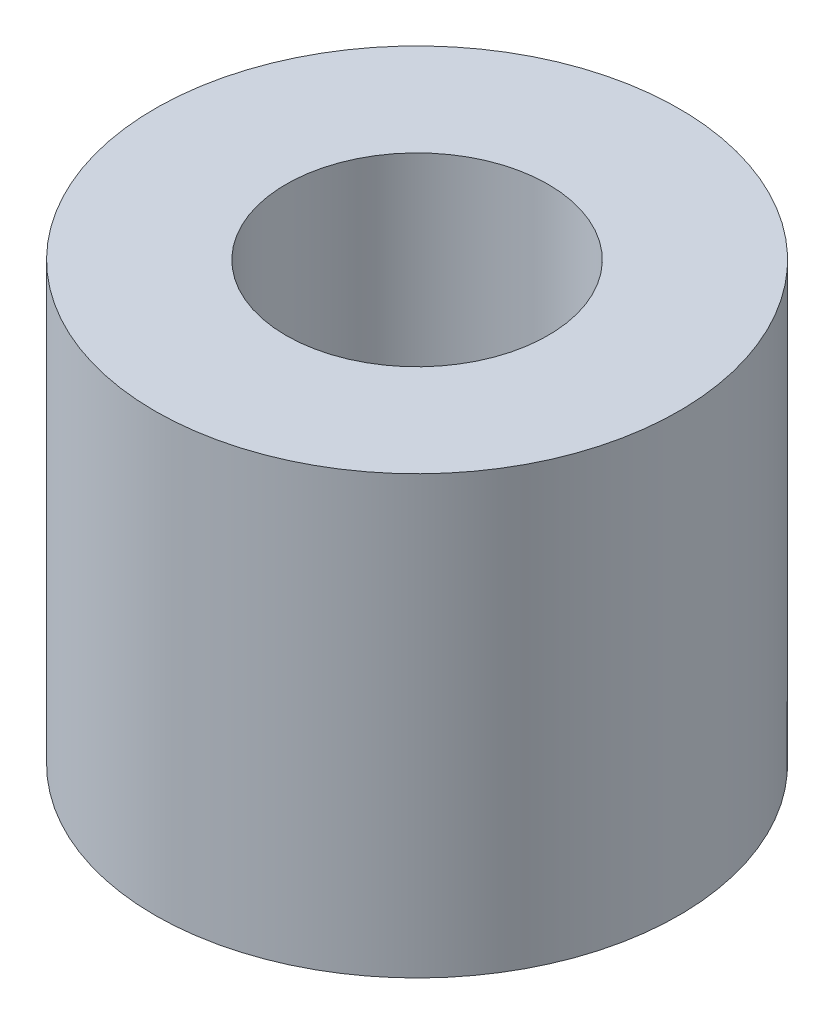
SolidWorks part; units mm, degrees
ref_plane "Front Plane" through (0, 0, 0) normal (0, 0, 1) x (1, 0, 0)
ref_plane "Top Plane" through (0, 0, 0) normal (0, 1, 0) x (1, 0, 0)
ref_plane "Right Plane" through (0, 0, 0) normal (1, 0, 0) x (0, 0, -1)
sketch "Sketch1" plane through (0, 0, 0) normal (0, 1, 0) x (1, 0, 0)
  circle A0 centre (0, 0) radius 3
extrude "Boss-Extrude1" add sketch "Sketch1" along normal blind 5 contours A0
sketch "Sketch2" plane through (0, 5, 0) normal (0, 1, 0) x (1, 0, 0)
  circle A0 centre (0, 0) radius 1.5
extrude "Cut-Extrude1" cut sketch "Sketch2" against normal blind 4
